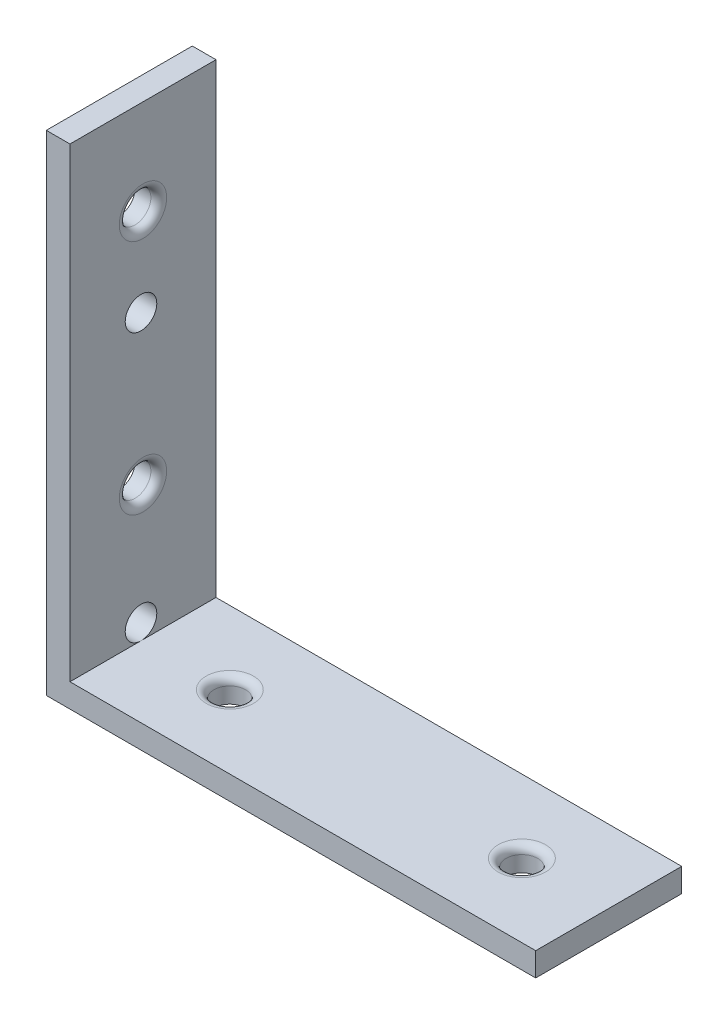
SolidWorks part; units mm, degrees
ref_plane "Front Plane" through (0, 0, 0) normal (0, 0, 1) x (1, 0, 0)
ref_plane "Top Plane" through (0, 0, 0) normal (0, 1, 0) x (1, 0, 0)
ref_plane "Right Plane" through (0, 0, 0) normal (1, 0, 0) x (0, 0, -1)
sketch "Sketch1" plane through (0, 0, 0) normal (0, 0, 1) x (1, 0, 0)
  line L1 (-31, 31) -> (31, 31)
  line L2 (-31, 31) -> (-31, -31)
  line L3 (-31, -31) -> (31, -31)
  line L4 (31, 31) -> (31, -31)
  line L5 (-31, 31) -> (31, -31) construction
  line L6 (-31, -31) -> (31, 31) construction
  point P0 (0, 0)
extrude "Boss-Extrude1" add sketch "Sketch1" along normal blind 18.5
sketch "Sketch2" plane through (0, 0, 18.5) normal (0, 0, 1) x (1, 0, 0)
  line L1 (31, 31) -> (-28, 31)
  line L2 (31, 31) -> (31, -28)
  line L3 (31, -28) -> (-28, -28)
  line L4 (-28, 31) -> (-28, -28)
extrude "Cut-Extrude1" cut sketch "Sketch2" against normal blind 18.5
sketch "Sketch3" plane through (0, -28, 0) normal (0, 1, 0) x (1, 0, 0)
  circle A0 centre (-17, -9.25) radius 2
extrude "Cut-Extrude2" cut sketch "Sketch3" against normal blind 3
sketch "Sketch4" plane through (0, -28, 0) normal (0, 1, 0) x (1, 0, 0)
  circle A0 centre (20, -9.25) radius 2
extrude "Cut-Extrude3" cut sketch "Sketch4" against normal blind 3 contours A0
fillet "Fillet1" radius 1 1 edges at (18, -28, 9.25)
fillet "Fillet2" radius 1 1 edges at (-19, -28, 9.25)
sketch "Sketch5" plane through (-28, 0, 0) normal (1, 0, 0) x (0, 0, -1)
  circle A0 centre (-9.25, -11) radius 2
extrude "Cut-Extrude4" cut sketch "Sketch5" against normal blind 3
sketch "Sketch6" plane through (-28, 0, 0) normal (1, 0, 0) x (0, 0, -1)
  circle A0 centre (-9.25, 19) radius 2
extrude "Cut-Extrude5" cut sketch "Sketch6" against normal blind 3
fillet "Fillet3" radius 1 1 edges at (-28, 21, 9.25)
fillet "Fillet4" radius 1 1 edges at (-28, -9, 9.25)
sketch "Sketch7" plane through (-28, 0, 0) normal (1, 0, 0) x (0, 0, -1)
  circle A0 centre (-9.5, -26) radius 2
extrude "Cut-Extrude6" cut sketch "Sketch7" against normal blind 3
sketch "Sketch8" plane through (-28, 0, 0) normal (1, 0, 0) x (0, 0, -1)
  circle A0 centre (-9.5, 8) radius 2
extrude "Cut-Extrude7" cut sketch "Sketch8" against normal blind 3
